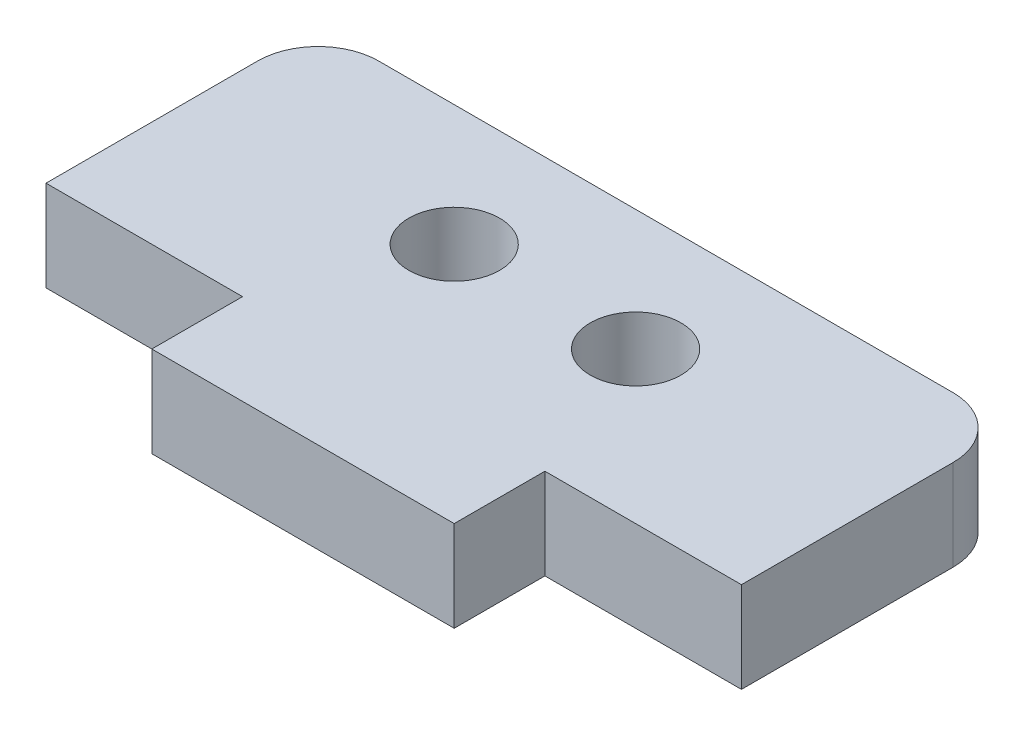
SolidWorks part; units mm, degrees
ref_plane "Front Plane" through (0, 0, 0) normal (0, 0, 1) x (1, 0, 0)
ref_plane "Top Plane" through (0, 0, 0) normal (0, 1, 0) x (1, 0, 0)
ref_plane "Right Plane" through (0, 0, 0) normal (1, 0, 0) x (0, 0, -1)
sketch "Sketch1" plane through (0, 0, 0) normal (0, 1, 0) x (1, 0, 0)
  line L0 (-4.6297, -2.3742) -> (-13.1297, -2.3742) construction
  line L1 (-11.1297, 1.6258) -> (7.8703, 1.6258)
  line L2 (-13.1297, -0.3742) -> (-13.1297, -7.3742)
  line L3 (-6.6297, -10.3742) -> (3.3703, -10.3742)
  line L4 (9.8703, -0.3742) -> (9.8703, -7.3742)
  line L5 (1.3703, -2.3742) -> (9.8703, -2.3742) construction
  line L6 (-13.1297, -7.3742) -> (-6.6297, -7.3742)
  line L7 (-6.6297, -7.3742) -> (-6.6297, -10.3742)
  line L8 (3.3703, -7.3742) -> (9.8703, -7.3742)
  line L9 (3.3703, -7.3742) -> (3.3703, -10.3742)
  circle A0 centre (-4.6297, -2.3742) radius 1.5
  circle A1 centre (1.3703, -2.3742) radius 1.5
  arc A2 (7.8703, 1.6258) -> (9.8703, -0.3742) centre (7.8703, -0.3742) cw
  arc A3 (-11.1297, 1.6258) -> (-13.1297, -0.3742) centre (-11.1297, -0.3742) ccw
  point P15 (9.8703, 1.6258)
  point P19 (-13.1297, 1.6258)
  dimension "D3" = 3
  dimension "D8" = 2
  dimension "D1" = 23
  dimension "D2" = 10
  dimension "D4" = 6
  dimension "D5" = 4
  dimension "D6" = 3
  dimension "D7" = 9
extrude "Boss-Extrude1" add sketch "Sketch1" along normal blind 3
